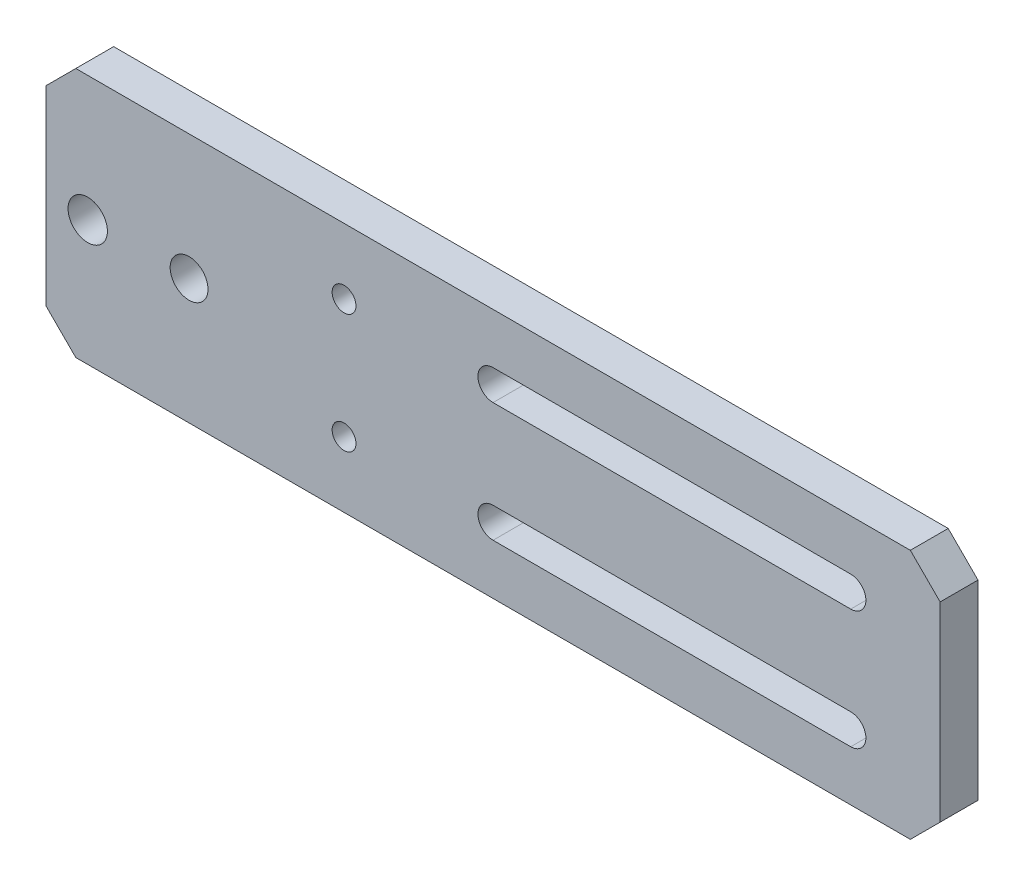
SolidWorks part; units mm, degrees
ref_plane "Front Plane" through (0, 0, 0) normal (0, 0, 1) x (1, 0, 0)
ref_plane "Top Plane" through (0, 0, 0) normal (0, 1, 0) x (1, 0, 0)
ref_plane "Right Plane" through (0, 0, 0) normal (1, 0, 0) x (0, 0, -1)
sketch "Sketch1" plane through (0, 0, 0) normal (0, 0, 1) x (1, 0, 0)
  line L1 (-100, 21) -> (100, 21)
  line L2 (-100, 21) -> (-100, -21)
  line L3 (-100, -21) -> (100, -21)
  line L4 (100, 21) -> (100, -21)
  line L5 (-100, 21) -> (100, -21) construction
  line L6 (-100, -21) -> (100, 21) construction
  point P0 (0, 0)
  dimension "D1" = 200
  dimension "D2" = 42
extrude "Boss-Extrude1" add sketch "Sketch1" along normal blind 6.35
sketch "Sketch3" plane through (0, 0, 6.35) normal (0, 0, 1) x (1, 0, 0)
  line L0 (-50, 10) -> (-50, -10) construction
  line L1 (-100, 21) -> (-100, -21) construction
  circle A0 centre (-50, 10) radius 2
  circle A1 centre (-50, -10) radius 2
  point P4 (-50, 0)
  dimension "D1" = 4
  dimension "D2" = 20
  dimension "D3" = 50
extrude "Cut-Extrude2" cut sketch "Sketch3" against normal through all
sketch "Sketch4" plane through (0, 0, 6.35) normal (0, 0, 1) x (1, 0, 0)
  line L0 (-100, 21) -> (-100, -21) construction
  line L1 (100, -21) -> (100, 21) construction
  circle A0 centre (-76, 0) radius 3.175
  circle A1 centre (80, 0) radius 3.175 construction
  dimension "D2" = 6.35
  dimension "D3" = 20
  dimension "D1" = 24
  dimension "D4" = 156
extrude "Cut-Extrude3" cut sketch "Sketch4" against normal through all
chamfer "Chamfer1" distance 5 angle 45 4 edges at (-100, 21, 3.175) (-100, -21, 3.175) (100, 21, 3.175) (100, -21, 3.175)
sketch "Sketch5" [suppressed] plane through (0, 0, 6.35) normal (0, 0, 1) x (1, 0, 0)
  line L0 (100, -16) -> (100, 16) construction
  circle A0 centre (77, 0) radius 11
  dimension "D1" = 22
  dimension "D2" = 23
extrude "Cut-Extrude4" [suppressed] cut sketch "Sketch5" against normal blind 25
sketch "Sketch7" [suppressed] plane through (0, 0, 6.35) normal (0, 0, 1) x (1, 0, 0)
  line L4 (7.5, 3.175) -> (-7.5, 3.175)
  line L5 (7.5, -3.175) -> (7.5, 3.175)
  line L6 (-7.5, -3.175) -> (7.5, -3.175)
  line L7 (-7.5, 3.175) -> (-7.5, -3.175)
  line L8 (7.5, 3.175) -> (-7.5, 3.175)
  line L9 (7.5, -3.175) -> (7.5, 3.175)
  line L10 (-7.5, -3.175) -> (7.5, -3.175)
  line L11 (-7.5, 3.175) -> (-7.5, -3.175)
  dimension "D1" = 0
extrude "Cut-Extrude6" [suppressed] cut sketch "Sketch7" against normal through all
sketch "Sketch8" [suppressed] plane through (0, 0, 6.35) normal (0, 0, 1) x (1, 0, 0)
  line L4 (25.5, 3.175) -> (10.5, 3.175)
  line L5 (10.5, 3.175) -> (10.5, -3.175)
  line L6 (10.5, -3.175) -> (25.5, -3.175)
  line L7 (25.5, -3.175) -> (25.5, 3.175)
  line L8 (25.5, 3.175) -> (10.5, 3.175)
  line L9 (10.5, 3.175) -> (10.5, -3.175)
  line L10 (10.5, -3.175) -> (25.5, -3.175)
  line L11 (25.5, -3.175) -> (25.5, 3.175)
  dimension "D1" = 0
extrude "Cut-Extrude7" [suppressed] cut sketch "Sketch8" against normal through all
sketch "Sketch9" plane through (0, 0, 6.35) normal (0, 0, 1) x (1, 0, 0)
  circle A0 centre (80, 0) radius 3.175 construction
  circle A1 centre (80, 0) radius 3.175
extrude "Cut-Extrude8" cut sketch "Sketch9" against normal through all
sketch "Sketch10" plane through (0, 0, 6.35) normal (0, 0, 1) x (1, 0, 0)
  circle A0 centre (80, 0) radius 12.5
  dimension "D1" = 25
extrude "Cut-Extrude9" cut sketch "Sketch10" against normal through all
sketch "Sketch11" [suppressed] plane through (0, 0, 6.35) normal (0, 0, 1) x (1, 0, 0)
  circle A0 centre (95.5563, 15.5563) radius 1.5 construction
  circle A1 centre (64.4437, 15.5563) radius 1.5 construction
  circle A2 centre (95.5563, -15.5563) radius 1.5 construction
  circle A3 centre (64.4437, -15.5563) radius 1.5 construction
  circle A4 centre (95.5563, 15.5563) radius 1.5
  circle A5 centre (64.4437, 15.5563) radius 1.5
  circle A6 centre (95.5563, -15.5563) radius 1.5
  circle A7 centre (64.4437, -15.5563) radius 1.5
extrude "Cut-Extrude10" [suppressed] cut sketch "Sketch11" against normal through all
sketch "Sketch12" plane through (0, 0, 6.35) normal (0, 0, 1) x (1, 0, 0)
  line L0 (-100, 16) -> (-100, -16) construction
  circle A0 centre (-93, 0) radius 3.302
  point P4 (-100, 0)
  dimension "D1" = 6.604
  dimension "D2" = 7
extrude "Cut-Extrude11" cut sketch "Sketch12" against normal through all
sketch "Sketch13" plane through (0, 0, 6.35) normal (0, 0, 1) x (1, 0, 0)
  line L0 (50, 16) -> (50, -16)
  line L1 (95, 21) -> (-95, 21) construction
  line L2 (-95, -21) -> (95, -21) construction
  line L3 (-100, 16) -> (-100, -16) construction
  line L4 (45, 21) -> (50, 16)
  line L5 (50, -16) -> (45, -21)
  line L6 (-95, -21) -> (95, -21)
  line L7 (95, 21) -> (-95, 21)
  line L8 (0, 0) -> (50, 0) construction
  line L9 (-25, 10) -> (35, 10) construction
  line L10 (-25, 12.54) -> (35, 12.54)
  line L11 (-25, 7.46) -> (35, 7.46)
  line L12 (95, 21) -> (-95, 21)
  line L13 (-95, 21) -> (-100, 16)
  line L14 (-100, 16) -> (-100, -16)
  line L15 (-100, -16) -> (-95, -21)
  line L16 (-95, -21) -> (95, -21)
  line L17 (95, -21) -> (100, -16)
  line L18 (100, -16) -> (100, 16)
  line L19 (100, 16) -> (95, 21)
  line L20 (45, 21) -> (-95, 21)
  line L21 (-95, 21) -> (-100, 16)
  line L22 (-100, 16) -> (-100, -16)
  line L23 (-100, -16) -> (-95, -21)
  line L24 (-95, -21) -> (45, -21)
  line L25 (95, -21) -> (100, -16)
  line L26 (100, -16) -> (100, 16)
  line L27 (100, 16) -> (95, 21)
  line L28 (-25, -10) -> (35, -10) construction
  line L29 (-25, -12.54) -> (35, -12.54)
  line L30 (-25, -7.46) -> (35, -7.46)
  arc A0 (-25, 12.54) -> (-25, 7.46) centre (-25, 10) ccw
  arc A1 (35, 7.46) -> (35, 12.54) centre (35, 10) ccw
  arc A2 (-25, -12.54) -> (-25, -7.46) centre (-25, -10) cw
  arc A3 (35, -7.46) -> (35, -12.54) centre (35, -10) cw
  point P0 (50, 21)
  point P1 (50, -21)
  point P22 (5, 10)
  point P27 (25, 0)
  point P30 (5, -10)
  circle M19 centre (80, 0) radius 12.5
  line M23 (95, 21) -> (-95, 21)
  line M27 (-95, -21) -> (95, -21)
  line M28 (95, -21) -> (100, -16)
  line M29 (100, -16) -> (100, 16)
  line M30 (100, 16) -> (95, 21)
  dimension "D8" = 2.54
  dimension "D1" = 150
  dimension "D3" = 10
  dimension "D4" = 15
  dimension "D7" = 60
  dimension "D2" = 0
extrude "Cut-Extrude12" cut sketch "Sketch13" against normal blind 10 contours L0 L5 L4 M27 M28 M29 M30 M23 M19 | L11 A1 L10 A0 | A3 L30 A2 L29
